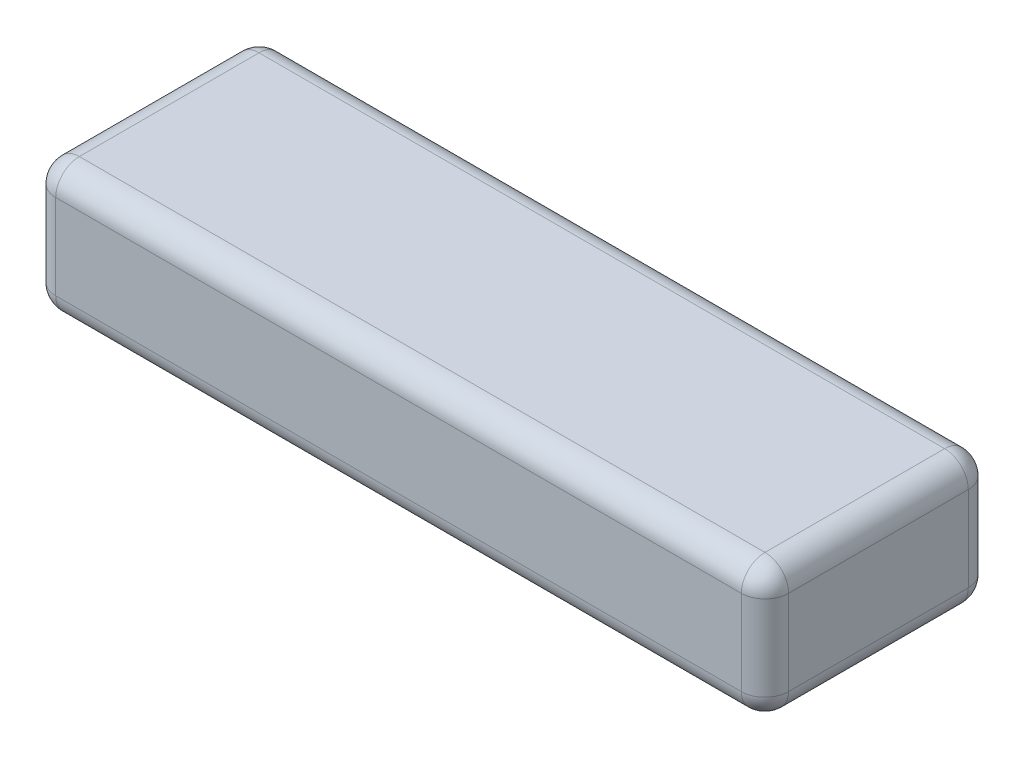
SolidWorks part; units mm, degrees
ref_plane "Ebene vorne" through (0, 0, 0) normal (0, 0, 1) x (1, 0, 0)
ref_plane "Ebene oben" through (0, 0, 0) normal (0, 1, 0) x (1, 0, 0)
ref_plane "Ebene rechts" through (0, 0, 0) normal (1, 0, 0) x (0, 0, -1)
sketch "Skizze1" plane through (0, 0, 0) normal (0, 1, 0) x (1, 0, 0)
  line L1 (0, 0) -> (155, 0)
  line L2 (0, 0) -> (0, 48)
  line L3 (0, 48) -> (155, 48)
  line L4 (155, 0) -> (155, 48)
  dimension "D1" = 155
  dimension "D2" = 48
extrude "Aufsatz-Linear austragen1" add sketch "Skizze1" along normal blind 28
fillet "Verrundung1" radius 5 12 edges at (77.5, 0, 0) (155, 0, -24) (77.5, 0, -48) (0, 0, -24) (0, 14, -48) (0, 14, 0) (155, 14, -48) (155, 14, 0) (155, 28, -24) (77.5, 28, -48) (0, 28, -24) (77.5, 28, 0)
